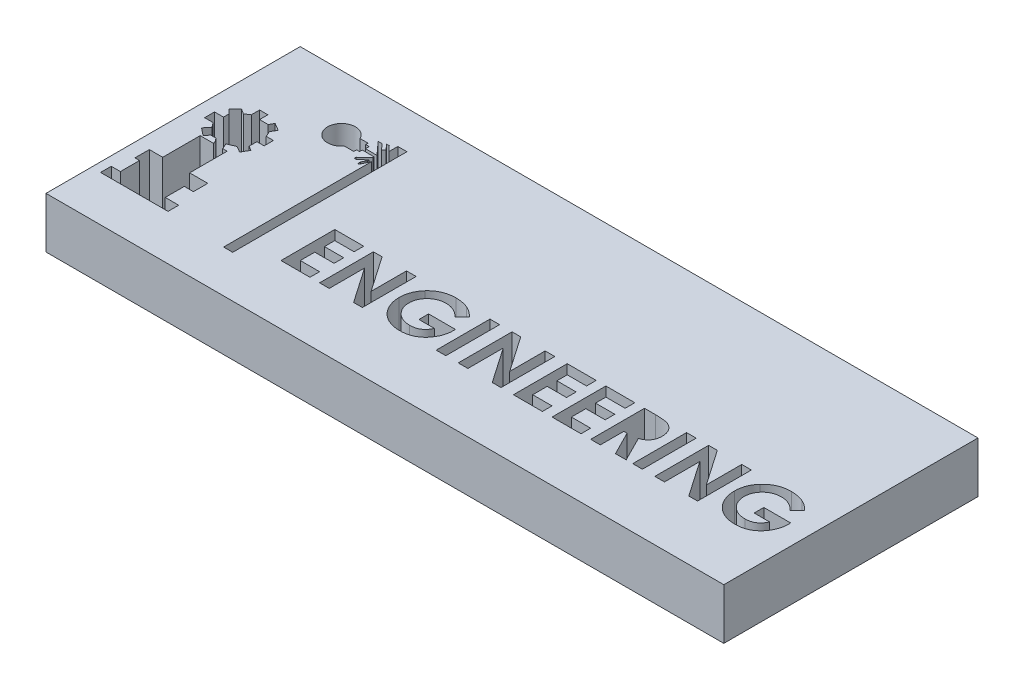
SolidWorks part; units mm, degrees
ref_plane "Front Plane" through (0, 0, 0) normal (0, 0, 1) x (1, 0, 0)
ref_plane "Top Plane" through (0, 0, 0) normal (0, 1, 0) x (1, 0, 0)
ref_plane "Right Plane" through (0, 0, 0) normal (1, 0, 0) x (0, 0, -1)
sketch "Sketch1" plane through (0, 0, 0) normal (0, 1, 0) x (1, 0, 0)
  line L0 (34.5946, 72.1622) -> (381.2613, 72.1622) construction
  line L1 (-20, -7.5) -> (20, -7.5)
  line L2 (-20, -7.5) -> (-20, 7.5)
  line L3 (-20, 7.5) -> (20, 7.5)
  line L4 (20, -7.5) -> (20, 7.5)
  line L5 (-20, -7.5) -> (20, 7.5) construction
  line L6 (-20, 7.5) -> (20, -7.5) construction
  line L7 (-19.4595, -4.8198) -> (-19.4595, -4.1892)
  line L8 (-19.4595, -4.1892) -> (-18.9195, -4.1892)
  line L9 (-18.9195, -4.1892) -> (-18.9195, -3.0641)
  line L10 (-18.9195, -3.0641) -> (-19.1895, -3.0641)
  line L11 (-19.1895, -3.0641) -> (-19.1895, -2.213)
  line L12 (-19.1895, -2.213) -> (-18.4014, -2.213)
  line L13 (-18.4014, -2.213) -> (-18.4014, 0)
  line L14 (-18.4014, 0) -> (-16.8102, 0)
  line L15 (-16.8102, 0) -> (-16.8102, -2.213)
  line L16 (-16.8102, -2.213) -> (-15.7371, -2.213)
  line L17 (-15.7371, -2.213) -> (-15.7371, -3.0641)
  line L18 (-15.7371, -3.0641) -> (-16.2737, -3.0641)
  line L19 (-16.2737, -3.0641) -> (-16.2737, -4.1892)
  line L20 (-16.2737, -4.1892) -> (-15.4781, -4.1892)
  line L21 (-15.4781, -4.1892) -> (-15.4781, -4.8198)
  line L22 (-15.4781, -4.8198) -> (-19.4595, -4.8198)
  line L23 (-19.1895, 1.1174) -> (-19.1895, 1.6354)
  line L24 (-19.1895, 1.6354) -> (-18.6604, 1.6354)
  line L25 (-18.6604, 1.6354) -> (-18.6604, 1.9685)
  line L26 (-18.6604, 1.9685) -> (-18.8958, 2.2038)
  line L27 (-18.8958, 2.2038) -> (-18.5259, 2.5737)
  line L28 (-18.5259, 2.5737) -> (-18.2402, 2.3888)
  line L29 (-18.2402, 2.3888) -> (-17.9574, 2.5737)
  line L30 (-17.9574, 2.4975) -> (-17.9574, 3.0626)
  line L31 (-17.9574, 3.0626) -> (-17.4688, 3.0626)
  line L32 (-17.4688, 3.0626) -> (-17.4688, 2.5737)
  line L33 (-17.4688, 2.5737) -> (-16.9641, 2.5737)
  line L34 (-16.9641, 2.5737) -> (-16.8102, 2.834)
  line L35 (-16.8102, 2.834) -> (-16.3697, 2.5737)
  line L36 (-16.3697, 2.5737) -> (-16.5612, 2.2496)
  line L37 (-16.5612, 2.2496) -> (-16.418, 1.9134)
  line L38 (-16.418, 1.9134) -> (-15.9922, 1.9134)
  line L39 (-15.9922, 1.9134) -> (-15.9922, 1.361)
  line L40 (-15.9922, 1.361) -> (-16.418, 1.361)
  line L41 (-16.418, 1.361) -> (-16.418, 0.9039)
  line L42 (-16.418, 0.9039) -> (-16.1479, 0.7443)
  line L43 (-16.1479, 0.7443) -> (-16.3971, 0.3226)
  line L44 (-16.3971, 0.3226) -> (-16.7538, 0.5335)
  line L45 (-16.7538, 0.5335) -> (-17.2164, 0.3365)
  line L46 (-17.2164, 0.3365) -> (-17.0731, 0)
  line L47 (-17.0731, 0) -> (-17.6058, 0)
  line L48 (-17.6058, 0) -> (-17.6775, 0.1683)
  line L49 (-17.6775, 0.1683) -> (-17.8039, 0.3365)
  line L50 (-17.8039, 0.3365) -> (-18.1162, 0.3365)
  line L51 (-18.1162, 0.3365) -> (-18.3179, 0.0841)
  line L52 (-18.3179, 0.0841) -> (-18.757, 0.435)
  line L53 (-18.757, 0.435) -> (-18.4828, 0.778)
  line L54 (-18.4828, 0.778) -> (-18.6845, 1.0463)
  line L55 (-18.6845, 1.0463) -> (-19.1895, 1.0463)
  line L56 (-19.1895, 1.0463) -> (-19.1895, 1.1174)
  line L57 (-16.9641, 3.0626) -> (-15.2759, 4.1847)
  line L58 (-16.2931, 1.9754) -> (-14.4464, 3.222)
  line L59 (-13.0604, 4.5697) -> (-13.5353, 4.5697)
  line L60 (-13.0604, 3.7219) -> (-13.6125, 3.7219)
  line L61 (-13.0604, 4.5697) -> (-13.0604, 4.428)
  line L62 (-13.0604, 4.428) -> (-12.8575, 4.428)
  line L63 (-12.8575, 4.428) -> (-12.8575, 4.2095)
  line L64 (-12.8575, 4.2095) -> (-12.1773, 4.2095)
  line L65 (-12.1773, 4.2095) -> (-12.8575, 4.9564)
  line L66 (-12.8575, 4.9564) -> (-12.6235, 4.9564)
  line L67 (-12.6235, 4.9564) -> (-12.3156, 4.6184)
  line L68 (-12.3156, 4.6184) -> (-12.1773, 4.7444)
  line L69 (-12.1773, 4.7444) -> (-12.4696, 5.0653)
  line L70 (-12.4696, 5.0653) -> (-12.3084, 5.0653)
  line L71 (-12.3084, 5.0653) -> (-12.0161, 4.7444)
  line L72 (-12.0161, 4.7444) -> (-12.0161, 5.2788)
  line L73 (-12.0161, 5.2788) -> (-11.4783, 5.2788)
  line L74 (-12.0161, 3.7219) -> (-12.0161, -5.0042)
  line L75 (-12.0161, -5.0042) -> (-11.4783, -5.0042)
  line L76 (-11.4783, 5.2788) -> (-11.4783, -5.0042)
  line L77 (-13.0604, 3.7219) -> (-13.0604, 3.8903)
  line L78 (-13.0604, 3.8903) -> (-12.8817, 3.8903)
  line L79 (-12.8817, 3.8903) -> (-12.8817, 4.0465)
  line L80 (-12.8817, 4.0465) -> (-12.1773, 4.0465)
  line L81 (-12.1773, 4.0465) -> (-12.1773, 3.9684)
  line L82 (-12.1773, 3.9684) -> (-12.6979, 3.4942)
  line L83 (-12.6979, 3.4942) -> (-12.6979, 3.388)
  line L84 (-12.6979, 3.388) -> (-12.5698, 3.388)
  line L85 (-12.5698, 3.388) -> (-12.1773, 3.7455)
  line L86 (-12.1773, 3.7455) -> (-12.1773, 3.6547)
  line L87 (-12.1773, 3.6547) -> (-12.3234, 3.388)
  line L88 (-12.3234, 3.388) -> (-12.3234, 3.222)
  line L89 (-12.3234, 3.222) -> (-12.2504, 3.222)
  line L90 (-12.2504, 3.222) -> (-12.0161, 3.7219)
  line L91 (-9.6337, -0.825) -> (-7.924, -0.825)
  line L92 (-7.924, -0.825) -> (-7.924, -1.3949)
  line L93 (-7.924, -1.3949) -> (-9.0638, -1.3949)
  line L94 (-9.0638, -1.3949) -> (-9.0638, -2.0054)
  line L95 (-9.0638, -2.0054) -> (-7.924, -2.0054)
  line L96 (-7.924, -2.0054) -> (-7.924, -2.5753)
  line L97 (-7.924, -2.5753) -> (-9.0638, -2.5753)
  line L98 (-9.0638, -2.5753) -> (-9.0638, -3.4301)
  line L99 (-9.0638, -3.4301) -> (-7.924, -3.4301)
  line L100 (-7.924, -3.4301) -> (-7.924, -4)
  line L101 (-7.924, -4) -> (-9.6337, -4)
  line L102 (-9.6337, -4) -> (-9.6337, -0.825)
  line L103 (-7.3542, -0.825) -> (-6.8409, -0.825)
  line L104 (-6.8409, -0.825) -> (-5.4003, -2.9143)
  line L105 (-5.4003, -2.9143) -> (-5.4003, -0.825)
  line L106 (-5.4003, -0.825) -> (-4.8304, -0.825)
  line L107 (-4.8304, -0.825) -> (-4.8304, -4)
  line L108 (-4.8304, -4) -> (-5.3475, -4)
  line L109 (-5.3475, -4) -> (-6.7843, -1.917)
  line L110 (-6.7843, -1.917) -> (-6.7843, -4)
  line L111 (-6.7843, -4) -> (-7.3542, -4)
  line L112 (-7.3542, -4) -> (-7.3542, -0.825)
  line L113 (-1.188, -1.33) -> (-1.6192, -1.7428)
  line L114 (-1.6395, -2.9417) -> (-2.551, -2.9417)
  line L115 (-2.551, -2.9417) -> (-2.551, -2.3718)
  line L116 (-2.551, -2.3718) -> (-0.9679, -2.3718)
  line L117 (-0.9679, -2.3718) -> (-0.9635, -2.5073)
  line L118 (-0.475, -0.825) -> (0.0949, -0.825)
  line L119 (0.0949, -0.825) -> (0.0949, -4)
  line L120 (0.0949, -4) -> (-0.475, -4)
  line L121 (-0.475, -4) -> (-0.475, -0.825)
  line L122 (0.8276, -0.825) -> (1.3408, -0.825)
  line L123 (1.3408, -0.825) -> (2.7814, -2.9143)
  line L124 (2.7814, -2.9143) -> (2.7814, -0.825)
  line L125 (2.7814, -0.825) -> (3.3513, -0.825)
  line L126 (3.3513, -0.825) -> (3.3513, -4)
  line L127 (3.3513, -4) -> (2.8342, -4)
  line L128 (2.8342, -4) -> (1.3974, -1.917)
  line L129 (1.3974, -1.917) -> (1.3974, -4)
  line L130 (1.3974, -4) -> (0.8276, -4)
  line L131 (0.8276, -4) -> (0.8276, -0.825)
  line L132 (4.084, -0.825) -> (5.7936, -0.825)
  line L133 (5.7936, -0.825) -> (5.7936, -1.3949)
  line L134 (5.7936, -1.3949) -> (4.6538, -1.3949)
  line L135 (4.6538, -1.3949) -> (4.6538, -2.0054)
  line L136 (4.6538, -2.0054) -> (5.7936, -2.0054)
  line L137 (5.7936, -2.0054) -> (5.7936, -2.5753)
  line L138 (5.7936, -2.5753) -> (4.6538, -2.5753)
  line L139 (4.6538, -2.5753) -> (4.6538, -3.4301)
  line L140 (4.6538, -3.4301) -> (5.7936, -3.4301)
  line L141 (5.7936, -3.4301) -> (5.7936, -4)
  line L142 (5.7936, -4) -> (4.084, -4)
  line L143 (4.084, -4) -> (4.084, -0.825)
  line L144 (6.3635, -0.825) -> (8.0731, -0.825)
  line L145 (8.0731, -0.825) -> (8.0731, -1.3949)
  line L146 (8.0731, -1.3949) -> (6.9333, -1.3949)
  line L147 (6.9333, -1.3949) -> (6.9333, -2.0054)
  line L148 (6.9333, -2.0054) -> (8.0731, -2.0054)
  line L149 (8.0731, -2.0054) -> (8.0731, -2.5753)
  line L150 (8.0731, -2.5753) -> (6.9333, -2.5753)
  line L151 (6.9333, -2.5753) -> (6.9333, -3.4301)
  line L152 (6.9333, -3.4301) -> (8.0731, -3.4301)
  line L153 (8.0731, -3.4301) -> (8.0731, -4)
  line L154 (8.0731, -4) -> (6.3635, -4)
  line L155 (6.3635, -4) -> (6.3635, -0.825)
  line L156 (8.6429, -0.825) -> (9.307, -0.825)
  line L157 (10.0066, -2.5512) -> (10.7393, -4)
  line L158 (10.7393, -4) -> (10.1058, -4)
  line L159 (10.1058, -4) -> (9.4062, -2.616)
  line L160 (9.4062, -2.616) -> (9.2128, -2.616)
  line L161 (9.2128, -2.616) -> (9.2128, -4)
  line L162 (9.2128, -4) -> (8.6429, -4)
  line L163 (8.6429, -4) -> (8.6429, -0.825)
  line L164 (9.2128, -2.0462) -> (9.4348, -2.0462)
  line L165 (9.4068, -1.3949) -> (9.2128, -1.3949)
  line L166 (9.2128, -1.3949) -> (9.2128, -2.0462)
  line L167 (11.126, -0.825) -> (11.6958, -0.825)
  line L168 (11.6958, -0.825) -> (11.6958, -4)
  line L169 (11.6958, -4) -> (11.126, -4)
  line L170 (11.126, -4) -> (11.126, -0.825)
  line L171 (12.4285, -0.825) -> (12.9418, -0.825)
  line L172 (12.9418, -0.825) -> (14.3824, -2.9143)
  line L173 (14.3824, -2.9143) -> (14.3824, -0.825)
  line L174 (14.3824, -0.825) -> (14.9522, -0.825)
  line L175 (14.9522, -0.825) -> (14.9522, -4)
  line L176 (14.9522, -4) -> (14.4352, -4)
  line L177 (14.4352, -4) -> (12.9984, -1.917)
  line L178 (12.9984, -1.917) -> (12.9984, -4)
  line L179 (12.9984, -4) -> (12.4285, -4)
  line L180 (12.4285, -4) -> (12.4285, -0.825)
  line L181 (18.5947, -1.33) -> (18.1635, -1.7428)
  line L182 (18.1431, -2.9417) -> (17.2317, -2.9417)
  line L183 (17.2317, -2.9417) -> (17.2317, -2.3718)
  line L184 (17.2317, -2.3718) -> (18.8148, -2.3718)
  line L185 (18.8148, -2.3718) -> (18.8192, -2.5073)
  arc A0 (-13.5353, 4.5697) -> (-13.6125, 3.7219) centre (-14.2737, 4.2095) ccw
  arc A1 (-15.2759, 4.1847) -> (-14.4464, 3.222) centre (-14.2737, 4.2095) ccw
  spline S0 degree 3 poles (-1.6192, -1.7428) (-1.6845, -1.6742) (-1.7893, -1.5806) (-1.9434, -1.48) (-2.0611, -1.419) (-2.1833, -1.3717) (-2.353, -1.326) (-2.4854, -1.3142) (-2.5739, -1.3135) knots 0 0 0 0 0.263807 0.389241 0.511496 0.632427 0.753439 1 1 1 1
  spline S1 degree 3 poles (-2.5739, -1.3135) (-2.6501, -1.3138) (-2.7632, -1.3224) (-2.9081, -1.3561) (-3.0107, -1.3905) (-3.1083, -1.4353) (-3.2012, -1.4897) (-3.2891, -1.5542) (-3.3712, -1.6276) (-3.4459, -1.7077) (-3.5112, -1.7935) (-3.5667, -1.8833) (-3.6125, -1.9776) (-3.6472, -2.0762) (-3.681, -2.2151) (-3.6908, -2.323) (-3.6907, -2.396) knots 0 0 0 0 0.131929 0.195189 0.257128 0.318843 0.380493 0.443219 0.507125 0.570712 0.632482 0.693253 0.753131 0.813458 0.873863 1 1 1 1
  spline S2 degree 3 poles (-3.6907, -2.396) (-3.6912, -2.4713) (-3.6806, -2.5828) (-3.6458, -2.7263) (-3.6082, -2.8277) (-3.562, -2.9254) (-3.5034, -3.0177) (-3.4351, -3.1059) (-3.3571, -3.1884) (-3.2723, -3.2645) (-3.1805, -3.3302) (-3.0844, -3.3868) (-2.9825, -3.4317) (-2.8766, -3.4677) (-2.7265, -3.5022) (-2.6096, -3.5115) (-2.5306, -3.5115) knots 0 0 0 0 0.125851 0.186472 0.246476 0.306258 0.366951 0.428861 0.492569 0.556606 0.619087 0.681049 0.742785 0.804896 0.867849 1 1 1 1
  spline S3 degree 3 poles (-2.5306, -3.5115) (-2.4794, -3.5123) (-2.4039, -3.5073) (-2.3062, -3.4926) (-2.2371, -3.4784) (-2.1716, -3.4583) (-2.1088, -3.4348) (-2.0491, -3.4071) (-1.9927, -3.3741) (-1.9389, -3.3372) (-1.8881, -3.295) (-1.8394, -3.2484) (-1.7935, -3.1969) (-1.7511, -3.1399) (-1.6963, -3.0565) (-1.6611, -2.9887) (-1.6395, -2.9417) knots 0 0 0 0 0.136147 0.200555 0.262794 0.323422 0.382464 0.440964 0.498292 0.555828 0.614284 0.673681 0.734765 0.797555 0.862276 1 1 1 1
  spline S4 degree 3 poles (-0.9635, -2.5073) (-0.9633, -2.5768) (-0.9697, -2.6808) (-0.9929, -2.8172) (-1.0166, -2.9179) (-1.0462, -3.0176) (-1.084, -3.1153) (-1.1283, -3.2118) (-1.1779, -3.3066) (-1.2337, -3.3975) (-1.2937, -3.4836) (-1.3571, -3.5648) (-1.4254, -3.6398) (-1.4973, -3.7093) (-1.5732, -3.7731) (-1.6532, -3.8312) (-1.7369, -3.8841) (-1.8248, -3.9305) (-1.9164, -3.9708) (-2.0116, -4.005) (-2.1106, -4.0331) (-2.2133, -4.0548) (-2.3572, -4.075) (-2.4675, -4.0817) (-2.5421, -4.0814) knots 0 0 0 0 0.083833 0.125322 0.166815 0.208475 0.250643 0.293094 0.336442 0.379594 0.421656 0.462988 0.503718 0.543863 0.583608 0.623143 0.663013 0.702932 0.742888 0.783652 0.824851 0.866926 0.910066 1 1 1 1
  spline S5 degree 3 poles (-2.5421, -4.0814) (-2.6223, -4.0815) (-2.7415, -4.0754) (-2.8969, -4.0522) (-3.0088, -4.0285) (-3.1176, -3.9989) (-3.2229, -3.9618) (-3.3248, -3.9177) (-3.4234, -3.8677) (-3.5174, -3.8111) (-3.6068, -3.7487) (-3.6909, -3.6802) (-3.7707, -3.6067) (-3.8442, -3.5265) (-3.9143, -3.4421) (-3.9775, -3.3505) (-4.0366, -3.2546) (-4.0891, -3.1544) (-4.135, -3.0518) (-4.1741, -2.9474) (-4.205, -2.8407) (-4.23, -2.7325) (-4.2541, -2.5847) (-4.2598, -2.472) (-4.2606, -2.3966) knots 0 0 0 0 0.089546 0.132813 0.175102 0.21703 0.25838 0.299576 0.340708 0.381538 0.421942 0.462115 0.502433 0.542752 0.583407 0.624663 0.666792 0.708988 0.750686 0.792055 0.833203 0.874439 0.915873 1 1 1 1
  spline S6 degree 3 poles (-4.2606, -2.3966) (-4.2611, -2.2943) (-4.248, -2.1425) (-4.2045, -1.9461) (-4.1586, -1.8058) (-4.0994, -1.6708) (-4.0036, -1.4952) (-3.9113, -1.3748) (-3.844, -1.2988) knots 0 0 0 0 0.255242 0.378902 0.501424 0.623259 0.746437 1 1 1 1
  spline S7 degree 3 poles (-3.844, -1.2988) (-3.8036, -1.253) (-3.7396, -1.1885) (-3.6489, -1.1094) (-3.5789, -1.0555) (-3.5066, -1.0054) (-3.4319, -0.9601) (-3.3551, -0.9181) (-3.2757, -0.8816) (-3.194, -0.8488) (-3.1098, -0.8211) (-3.0236, -0.7966) (-2.9346, -0.7779) (-2.8439, -0.7624) (-2.7182, -0.7482) (-2.6225, -0.7427) (-2.558, -0.7436) knots 0 0 0 0 0.126616 0.188343 0.249479 0.309864 0.370656 0.430675 0.491278 0.551874 0.613065 0.675167 0.737705 0.801473 0.866116 1 1 1 1
  spline S8 degree 3 poles (-2.558, -0.7436) (-2.49, -0.7438) (-2.3888, -0.7485) (-2.2553, -0.7636) (-2.1575, -0.7804) (-2.0612, -0.8011) (-1.9356, -0.8363) (-1.8434, -0.8687) (-1.7833, -0.8937) knots 0 0 0 0 0.256614 0.382375 0.50745 0.631232 0.754221 1 1 1 1
  spline S9 degree 3 poles (-1.7833, -0.8937) (-1.731, -0.915) (-1.6547, -0.954) (-1.5557, -1.0143) (-1.4809, -1.0661) (-1.4069, -1.124) (-1.3064, -1.2096) (-1.235, -1.2806) (-1.188, -1.33) knots 0 0 0 0 0.227396 0.345657 0.4674 0.594208 0.724678 1 1 1 1
  spline S10 degree 3 poles (9.307, -0.825) (9.3914, -0.8245) (9.5132, -0.8275) (9.6688, -0.8368) (9.7709, -0.8468) (9.8632, -0.8601) (9.9458, -0.8758) (10.0187, -0.8937) (10.0825, -0.916) (10.1401, -0.9411) (10.1938, -0.97) (10.2448, -1.0023) (10.2927, -1.0389) (10.338, -1.0791) (10.3807, -1.1229) (10.4202, -1.1708) (10.4563, -1.2224) (10.4893, -1.2767) (10.5184, -1.3337) (10.542, -1.3936) (10.5629, -1.4553) (10.578, -1.5199) (10.5923, -1.6104) (10.5977, -1.6798) (10.5968, -1.7269) knots 0 0 0 0 0.140186 0.202277 0.258895 0.310483 0.357095 0.398514 0.435038 0.469251 0.502805 0.53621 0.569379 0.602801 0.636666 0.670929 0.705803 0.741189 0.776304 0.812004 0.847969 0.884522 0.921974 1 1 1 1
  spline S11 degree 3 poles (10.5968, -1.7269) (10.596, -1.7759) (10.593, -1.8483) (10.5776, -1.942) (10.5605, -2.0077) (10.5409, -2.0708) (10.5148, -2.1303) (10.4853, -2.187) (10.4503, -2.24) (10.4119, -2.2907) (10.3673, -2.3369) (10.3193, -2.3813) (10.2652, -2.4211) (10.2074, -2.4588) (10.1223, -2.5054) (10.054, -2.5344) (10.0066, -2.5512) knots 0 0 0 0 0.134789 0.198536 0.260386 0.320962 0.379904 0.438503 0.496154 0.554265 0.612749 0.672513 0.733646 0.79679 0.861936 1 1 1 1
  spline S12 degree 3 poles (9.4348, -2.0462) (9.4867, -2.0454) (9.5616, -2.0451) (9.6565, -2.036) (9.7178, -2.0277) (9.7728, -2.0182) (9.8211, -2.0045) (9.8634, -1.9899) (9.8992, -1.9717) (9.9298, -1.951) (9.9562, -1.9274) (9.9781, -1.9002) (9.996, -1.87) (10.01, -1.8366) (10.0241, -1.7866) (10.0268, -1.7465) (10.0269, -1.7192) knots 0 0 0 0 0.202086 0.290685 0.370553 0.44267 0.507675 0.565573 0.616455 0.663331 0.708862 0.753412 0.798515 0.845064 0.893873 1 1 1 1
  spline S13 degree 3 poles (10.0269, -1.7192) (10.0273, -1.6862) (10.0195, -1.6371) (9.9923, -1.5777) (9.9649, -1.5374) (9.9302, -1.5021) (9.8905, -1.471) (9.8448, -1.4463) (9.8025, -1.4301) (9.764, -1.4204) (9.7293, -1.4131) (9.689, -1.408) (9.6433, -1.4025) (9.5921, -1.399) (9.5126, -1.3954) (9.4503, -1.3953) (9.4068, -1.3949) knots 0 0 0 0 0.125262 0.185414 0.246807 0.309422 0.372533 0.437733 0.50575 0.544013 0.58837 0.640389 0.697897 0.763272 0.834979 1 1 1 1
  spline S14 degree 3 poles (18.1635, -1.7428) (18.0982, -1.6742) (17.9934, -1.5806) (17.8393, -1.48) (17.7216, -1.419) (17.5994, -1.3717) (17.4297, -1.326) (17.2973, -1.3142) (17.2088, -1.3135) knots 0 0 0 0 0.263807 0.389241 0.511496 0.632427 0.753439 1 1 1 1
  spline S15 degree 3 poles (17.2088, -1.3135) (17.1326, -1.3138) (17.0195, -1.3224) (16.8746, -1.3561) (16.7719, -1.3905) (16.6744, -1.4353) (16.5814, -1.4897) (16.4936, -1.5542) (16.4115, -1.6276) (16.3368, -1.7077) (16.2715, -1.7935) (16.216, -1.8833) (16.1702, -1.9776) (16.1354, -2.0762) (16.1017, -2.2151) (16.0919, -2.323) (16.092, -2.396) knots 0 0 0 0 0.131929 0.195189 0.257128 0.318843 0.380493 0.443219 0.507125 0.570712 0.632482 0.693253 0.753131 0.813458 0.873863 1 1 1 1
  spline S16 degree 3 poles (16.092, -2.396) (16.0915, -2.4713) (16.1021, -2.5828) (16.1369, -2.7263) (16.1744, -2.8277) (16.2207, -2.9254) (16.2793, -3.0177) (16.3476, -3.1059) (16.4256, -3.1884) (16.5104, -3.2645) (16.6022, -3.3302) (16.6983, -3.3868) (16.8001, -3.4317) (16.906, -3.4677) (17.0562, -3.5022) (17.1731, -3.5115) (17.2521, -3.5115) knots 0 0 0 0 0.125851 0.186472 0.246476 0.306258 0.366951 0.428861 0.492569 0.556606 0.619087 0.681049 0.742785 0.804896 0.867849 1 1 1 1
  spline S17 degree 3 poles (17.2521, -3.5115) (17.3033, -3.5123) (17.3788, -3.5073) (17.4765, -3.4926) (17.5456, -3.4784) (17.6111, -3.4583) (17.6739, -3.4348) (17.7336, -3.4071) (17.79, -3.3741) (17.8438, -3.3372) (17.8946, -3.295) (17.9432, -3.2484) (17.9892, -3.1969) (18.0316, -3.1399) (18.0864, -3.0565) (18.1216, -2.9887) (18.1431, -2.9417) knots 0 0 0 0 0.136147 0.200555 0.262794 0.323422 0.382464 0.440964 0.498292 0.555828 0.614284 0.673681 0.734765 0.797555 0.862276 1 1 1 1
  spline S18 degree 3 poles (18.8192, -2.5073) (18.8194, -2.5768) (18.813, -2.6808) (18.7897, -2.8172) (18.7661, -2.9179) (18.7365, -3.0176) (18.6986, -3.1153) (18.6544, -3.2118) (18.6048, -3.3066) (18.549, -3.3975) (18.489, -3.4836) (18.4256, -3.5648) (18.3573, -3.6398) (18.2854, -3.7093) (18.2095, -3.7731) (18.1295, -3.8312) (18.0458, -3.8841) (17.9579, -3.9305) (17.8663, -3.9708) (17.7711, -4.005) (17.6721, -4.0331) (17.5694, -4.0548) (17.4255, -4.075) (17.3152, -4.0817) (17.2406, -4.0814) knots 0 0 0 0 0.083833 0.125322 0.166815 0.208475 0.250643 0.293094 0.336442 0.379594 0.421656 0.462988 0.503718 0.543863 0.583608 0.623143 0.663013 0.702932 0.742888 0.783652 0.824851 0.866926 0.910066 1 1 1 1
  spline S19 degree 3 poles (17.2406, -4.0814) (17.1603, -4.0815) (17.0412, -4.0754) (16.8858, -4.0522) (16.7739, -4.0285) (16.6651, -3.9989) (16.5597, -3.9618) (16.4579, -3.9177) (16.3593, -3.8677) (16.2653, -3.8111) (16.1759, -3.7487) (16.0918, -3.6802) (16.012, -3.6067) (15.9385, -3.5265) (15.8684, -3.4421) (15.8052, -3.3505) (15.7461, -3.2546) (15.6936, -3.1544) (15.6477, -3.0518) (15.6086, -2.9474) (15.5777, -2.8407) (15.5527, -2.7325) (15.5286, -2.5847) (15.5229, -2.472) (15.5221, -2.3966) knots 0 0 0 0 0.089546 0.132813 0.175102 0.21703 0.25838 0.299576 0.340708 0.381538 0.421942 0.462115 0.502433 0.542752 0.583407 0.624663 0.666792 0.708988 0.750686 0.792055 0.833203 0.874439 0.915873 1 1 1 1
  spline S20 degree 3 poles (15.5221, -2.3966) (15.5216, -2.2943) (15.5347, -2.1425) (15.5782, -1.9461) (15.6241, -1.8058) (15.6832, -1.6708) (15.7791, -1.4952) (15.8713, -1.3748) (15.9387, -1.2988) knots 0 0 0 0 0.255242 0.378902 0.501424 0.623259 0.746437 1 1 1 1
  spline S21 degree 3 poles (15.9387, -1.2988) (15.9791, -1.253) (16.0431, -1.1885) (16.1338, -1.1094) (16.2038, -1.0555) (16.2761, -1.0054) (16.3508, -0.9601) (16.4276, -0.9181) (16.507, -0.8816) (16.5887, -0.8488) (16.6729, -0.8211) (16.7591, -0.7966) (16.8481, -0.7779) (16.9388, -0.7624) (17.0645, -0.7482) (17.1601, -0.7427) (17.2247, -0.7436) knots 0 0 0 0 0.126616 0.188343 0.249479 0.309864 0.370656 0.430675 0.491278 0.551874 0.613065 0.675167 0.737705 0.801473 0.866116 1 1 1 1
  spline S22 degree 3 poles (17.2247, -0.7436) (17.2927, -0.7438) (17.3939, -0.7485) (17.5274, -0.7636) (17.6252, -0.7804) (17.7215, -0.8011) (17.8471, -0.8363) (17.9393, -0.8687) (17.9994, -0.8937) knots 0 0 0 0 0.256614 0.382375 0.50745 0.631232 0.754221 1 1 1 1
  spline S23 degree 3 poles (17.9994, -0.8937) (18.0517, -0.915) (18.128, -0.954) (18.227, -1.0143) (18.3018, -1.0661) (18.3758, -1.124) (18.4763, -1.2096) (18.5477, -1.2806) (18.5947, -1.33) knots 0 0 0 0 0.227396 0.345657 0.4674 0.594208 0.724678 1 1 1 1
  point P0 (0, 0)
  point P97 (0, 0)
  dimension "D1" = 40
  dimension "D2" = 15
extrude "Boss-Extrude1" add sketch "Sketch1" along normal blind 3
